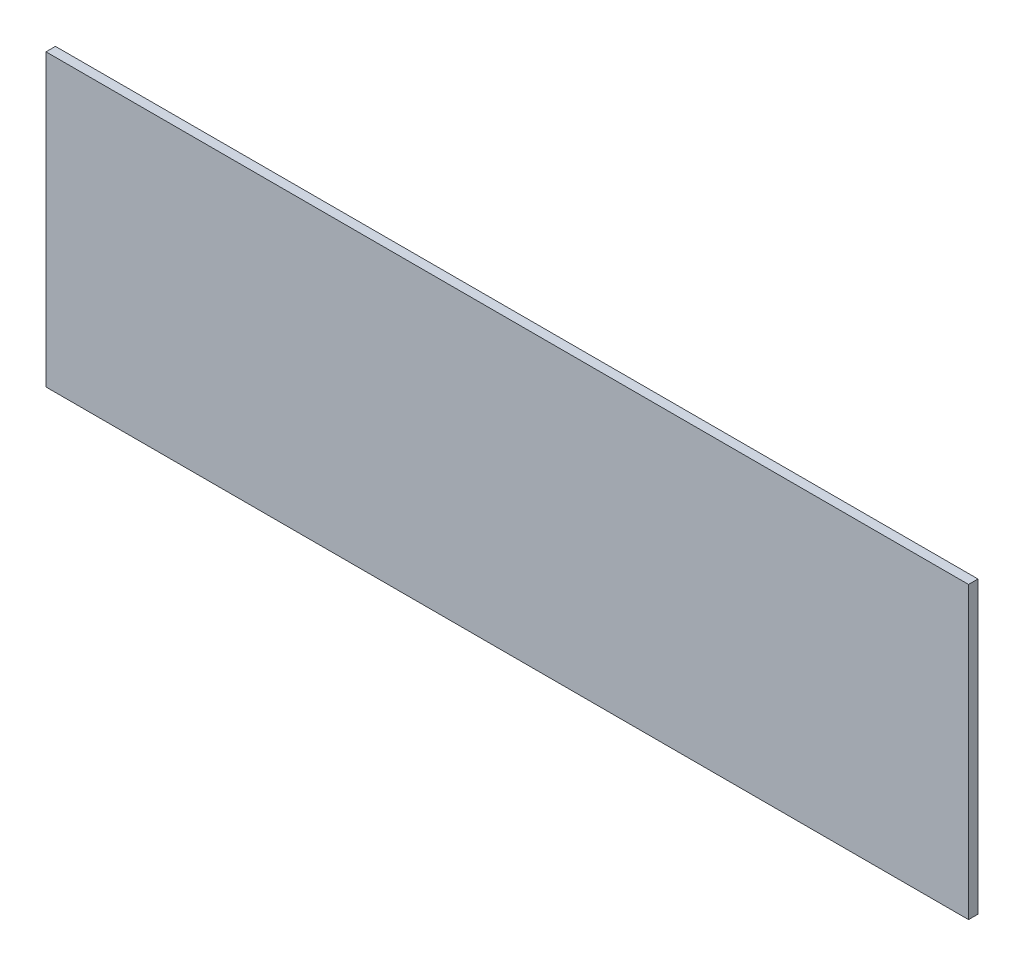
SolidWorks part; units mm, degrees
ref_plane "Front Plane" through (0, 0, 0) normal (0, 0, 1) x (1, 0, 0)
ref_plane "Top Plane" through (0, 0, 0) normal (0, 1, 0) x (1, 0, 0)
ref_plane "Right Plane" through (0, 0, 0) normal (1, 0, 0) x (0, 0, -1)
sketch "Sketch1" plane through (0, 0, 0) normal (0, 0, 1) x (1, 0, 0)
  line L1 (-73.25, -23.05) -> (73.25, -23.05)
  line L2 (-73.25, -23.05) -> (-73.25, 23.05)
  line L3 (-73.25, 23.05) -> (73.25, 23.05)
  line L4 (73.25, -23.05) -> (73.25, 23.05)
  line L5 (-73.25, -23.05) -> (73.25, 23.05) construction
  line L6 (-73.25, 23.05) -> (73.25, -23.05) construction
  point P0 (0, 0)
  dimension "D1" = 146.5
  dimension "D2" = 46.1
extrude "Boss-Extrude1" add sketch "Sketch1" along normal blind 1.5
